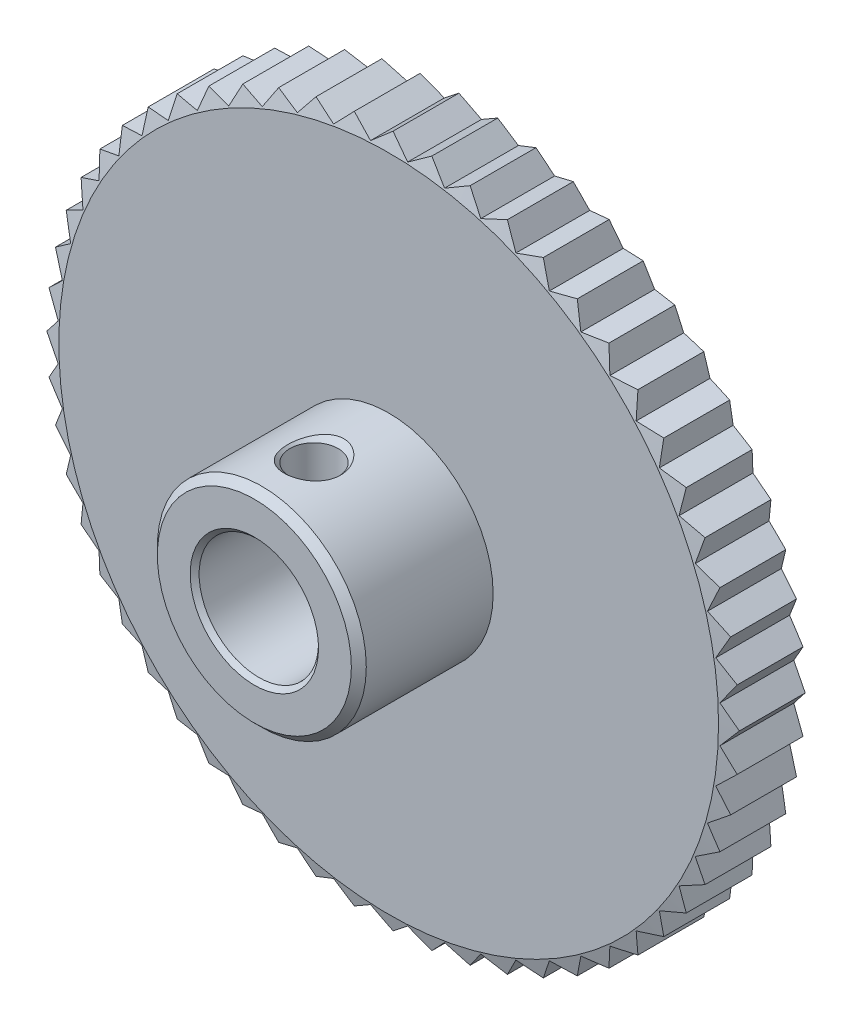
SolidWorks part; units mm, degrees
material "POM Acetal Copolymer"
ref_plane "Front Plane" through (0, 0, 0) normal (0, 0, 1) x (1, 0, 0)
ref_plane "Top Plane" through (0, 0, 0) normal (0, 1, 0) x (1, 0, 0)
ref_plane "Right Plane" through (0, 0, 0) normal (1, 0, 0) x (0, 0, -1)
ref_plane "Plane1" through (0, 0, 0) normal (1, 0, 0) x (0, 0, -1)
sketch "Sketch1" plane through (0, 0, 0) normal (1, 0, 0) x (0, 0, -1)
  line L0 (-14, 4.3) -> (-13.7, 4)
  line L1 (-13.7, 4) -> (-0.3, 4)
  line L2 (-0.3, 4) -> (0, 4.3)
  line L3 (0, 4.3) -> (0, 22.1)
  line L4 (0, 22.1) -> (-0.5627, 24.2)
  line L5 (-0.5627, 24.2) -> (-4.4373, 24.2)
  line L6 (-4.4373, 24.2) -> (-5, 22.1)
  line L7 (-5, 22.1) -> (-5, 7)
  line L8 (-5, 7) -> (-13.5, 7)
  line L9 (-13.5, 7) -> (-14, 6.5)
  line L10 (-14, 6.5) -> (-14, 4.3)
  line L11 (0, 0) -> (-14, 0) construction
revolve "Revolve1" add sketch "Sketch1" angle 360 about L11
ref_plane "Plane2" through (0, 0, 0) normal (0, 0, 1) x (1, 0, 0)
sketch "Sketch2" plane through (0, 0, 0) normal (0, 0, 1) x (1, 0, 0)
  line L0 (-23.2, 0) -> (-22.1651, -1.2448)
  line L1 (-22.1651, -1.2448) -> (-23.0541, -2.5976)
  line L2 (-23.0541, -2.5976) -> (-21.8863, -3.7186)
  line L3 (-21.8863, -3.7186) -> (-22.6183, -5.1625)
  line L4 (-22.6183, -5.1625) -> (-21.3324, -6.1457)
  line L5 (-21.3324, -6.1457) -> (-21.8981, -7.6625)
  line L6 (-21.8981, -7.6625) -> (-20.5101, -8.4956)
  line L7 (-20.5101, -8.4956) -> (-20.9025, -10.0661)
  line L8 (-20.9025, -10.0661) -> (-19.43, -10.7386)
  line L9 (-19.43, -10.7386) -> (-19.644, -12.3431)
  line L10 (-19.644, -12.3431) -> (-18.1055, -12.8465)
  line L11 (-18.1055, -12.8465) -> (-18.1385, -14.465)
  line L12 (-18.1385, -14.465) -> (-16.5533, -14.7929)
  line L13 (-16.5533, -14.7929) -> (-16.4049, -16.4049)
  line L14 (-16.4049, -16.4049) -> (-14.7929, -16.5533)
  line L15 (-14.7929, -16.5533) -> (-14.465, -18.1385)
  line L16 (-14.465, -18.1385) -> (-12.8465, -18.1055)
  line L17 (-12.8465, -18.1055) -> (-12.3431, -19.644)
  line L18 (-12.3431, -19.644) -> (-10.7386, -19.43)
  line L19 (-10.7386, -19.43) -> (-10.0661, -20.9025)
  line L20 (-10.0661, -20.9025) -> (-8.4956, -20.5101)
  line L21 (-8.4956, -20.5101) -> (-7.6625, -21.8981)
  line L22 (-7.6625, -21.8981) -> (-6.1457, -21.3324)
  line L23 (-6.1457, -21.3324) -> (-5.1625, -22.6183)
  line L24 (-5.1625, -22.6183) -> (-3.7186, -21.8863)
  line L25 (-3.7186, -21.8863) -> (-2.5976, -23.0541)
  line L26 (-2.5976, -23.0541) -> (-1.2448, -22.1651)
  line L27 (-1.2448, -22.1651) -> (0, -23.2)
  line L28 (0, -23.2) -> (1.2448, -22.1651)
  line L29 (1.2448, -22.1651) -> (2.5976, -23.0541)
  line L30 (2.5976, -23.0541) -> (3.7186, -21.8863)
  line L31 (3.7186, -21.8863) -> (5.1625, -22.6183)
  line L32 (5.1625, -22.6183) -> (6.1457, -21.3324)
  line L33 (6.1457, -21.3324) -> (7.6625, -21.8981)
  line L34 (7.6625, -21.8981) -> (8.4956, -20.5101)
  line L35 (8.4956, -20.5101) -> (10.0661, -20.9025)
  line L36 (10.0661, -20.9025) -> (10.7386, -19.43)
  line L37 (10.7386, -19.43) -> (12.3431, -19.644)
  line L38 (12.3431, -19.644) -> (12.8465, -18.1055)
  line L39 (12.8465, -18.1055) -> (14.465, -18.1385)
  line L40 (14.465, -18.1385) -> (14.7929, -16.5533)
  line L41 (14.7929, -16.5533) -> (16.4049, -16.4049)
  line L42 (16.4049, -16.4049) -> (16.5533, -14.7929)
  line L43 (16.5533, -14.7929) -> (18.1385, -14.465)
  line L44 (18.1385, -14.465) -> (18.1055, -12.8465)
  line L45 (18.1055, -12.8465) -> (19.644, -12.3431)
  line L46 (19.644, -12.3431) -> (19.43, -10.7386)
  line L47 (19.43, -10.7386) -> (20.9025, -10.0661)
  line L48 (20.9025, -10.0661) -> (20.5101, -8.4956)
  line L49 (20.5101, -8.4956) -> (21.8981, -7.6625)
  line L50 (21.8981, -7.6625) -> (21.3324, -6.1457)
  line L51 (21.3324, -6.1457) -> (22.6183, -5.1625)
  line L52 (22.6183, -5.1625) -> (21.8863, -3.7186)
  line L53 (21.8863, -3.7186) -> (23.0541, -2.5976)
  line L54 (23.0541, -2.5976) -> (22.1651, -1.2448)
  line L55 (22.1651, -1.2448) -> (23.2, 0)
  line L56 (23.2, 0) -> (22.1651, 1.2448)
  line L57 (22.1651, 1.2448) -> (23.0541, 2.5976)
  line L58 (23.0541, 2.5976) -> (21.8863, 3.7186)
  line L59 (21.8863, 3.7186) -> (22.6183, 5.1625)
  line L60 (22.6183, 5.1625) -> (21.3324, 6.1457)
  line L61 (21.3324, 6.1457) -> (21.8981, 7.6625)
  line L62 (21.8981, 7.6625) -> (20.5101, 8.4956)
  line L63 (20.5101, 8.4956) -> (20.9025, 10.0661)
  line L64 (20.9025, 10.0661) -> (19.43, 10.7386)
  line L65 (19.43, 10.7386) -> (19.644, 12.3431)
  line L66 (19.644, 12.3431) -> (18.1055, 12.8465)
  line L67 (18.1055, 12.8465) -> (18.1385, 14.465)
  line L68 (18.1385, 14.465) -> (16.5533, 14.7929)
  line L69 (16.5533, 14.7929) -> (16.4049, 16.4049)
  line L70 (16.4049, 16.4049) -> (14.7929, 16.5533)
  line L71 (14.7929, 16.5533) -> (14.465, 18.1385)
  line L72 (14.465, 18.1385) -> (12.8465, 18.1055)
  line L73 (12.8465, 18.1055) -> (12.3431, 19.644)
  line L74 (12.3431, 19.644) -> (10.7386, 19.43)
  line L75 (10.7386, 19.43) -> (10.0661, 20.9025)
  line L76 (10.0661, 20.9025) -> (8.4956, 20.5101)
  line L77 (8.4956, 20.5101) -> (7.6625, 21.8981)
  line L78 (7.6625, 21.8981) -> (6.1457, 21.3324)
  line L79 (6.1457, 21.3324) -> (5.1625, 22.6183)
  line L80 (5.1625, 22.6183) -> (3.7186, 21.8863)
  line L81 (3.7186, 21.8863) -> (2.5976, 23.0541)
  line L82 (2.5976, 23.0541) -> (1.2448, 22.1651)
  line L83 (1.2448, 22.1651) -> (0, 23.2)
  line L84 (0, 23.2) -> (-1.2448, 22.1651)
  line L85 (-1.2448, 22.1651) -> (-2.5976, 23.0541)
  line L86 (-2.5976, 23.0541) -> (-3.7186, 21.8863)
  line L87 (-3.7186, 21.8863) -> (-5.1625, 22.6183)
  line L88 (-5.1625, 22.6183) -> (-6.1457, 21.3324)
  line L89 (-6.1457, 21.3324) -> (-7.6625, 21.8981)
  line L90 (-7.6625, 21.8981) -> (-8.4956, 20.5101)
  line L91 (-8.4956, 20.5101) -> (-10.0661, 20.9025)
  line L92 (-10.0661, 20.9025) -> (-10.7386, 19.43)
  line L93 (-10.7386, 19.43) -> (-12.3431, 19.644)
  line L94 (-12.3431, 19.644) -> (-12.8465, 18.1055)
  line L95 (-12.8465, 18.1055) -> (-14.465, 18.1385)
  line L96 (-14.465, 18.1385) -> (-14.7929, 16.5533)
  line L97 (-14.7929, 16.5533) -> (-16.4049, 16.4049)
  line L98 (-16.4049, 16.4049) -> (-16.5533, 14.7929)
  line L99 (-16.5533, 14.7929) -> (-18.1385, 14.465)
  line L100 (-18.1385, 14.465) -> (-18.1055, 12.8465)
  line L101 (-18.1055, 12.8465) -> (-19.644, 12.3431)
  line L102 (-19.644, 12.3431) -> (-19.43, 10.7386)
  line L103 (-19.43, 10.7386) -> (-20.9025, 10.0661)
  line L104 (-20.9025, 10.0661) -> (-20.5101, 8.4956)
  line L105 (-20.5101, 8.4956) -> (-21.8981, 7.6625)
  line L106 (-21.8981, 7.6625) -> (-21.3324, 6.1457)
  line L107 (-21.3324, 6.1457) -> (-22.6183, 5.1625)
  line L108 (-22.6183, 5.1625) -> (-21.8863, 3.7186)
  line L109 (-21.8863, 3.7186) -> (-23.0541, 2.5976)
  line L110 (-23.0541, 2.5976) -> (-22.1651, 1.2448)
  line L111 (-22.1651, 1.2448) -> (-23.2, 0)
  circle A0 centre (0, 0) radius 46.4
extrude "Cut-Extrude1" cut sketch "Sketch2" along normal blind 5
ref_plane "Plane3" through (0, 0, 10) normal (0, 0, 1) x (1, 0, 0)
sketch "Sketch3" plane through (0, 0, 10) normal (0, 0, 1) x (1, 0, 0)
  line L0 (0, 0) -> (-2, 0)
  line L1 (-2, 0) -> (-2, 4)
  line L2 (-2, 4) -> (-1.621, 4.379)
  line L3 (-1.621, 4.379) -> (-1.621, 6.621)
  line L4 (-1.621, 6.621) -> (-2, 7)
  line L5 (-2, 7) -> (-2, 15)
  line L6 (-2, 15) -> (0, 15)
  line L7 (0, 15) -> (0, 0)
  line L8 (0, 15) -> (0, 0) construction
revolve "Cut-Revolve1" cut sketch "Sketch3" angle 360 about L8
